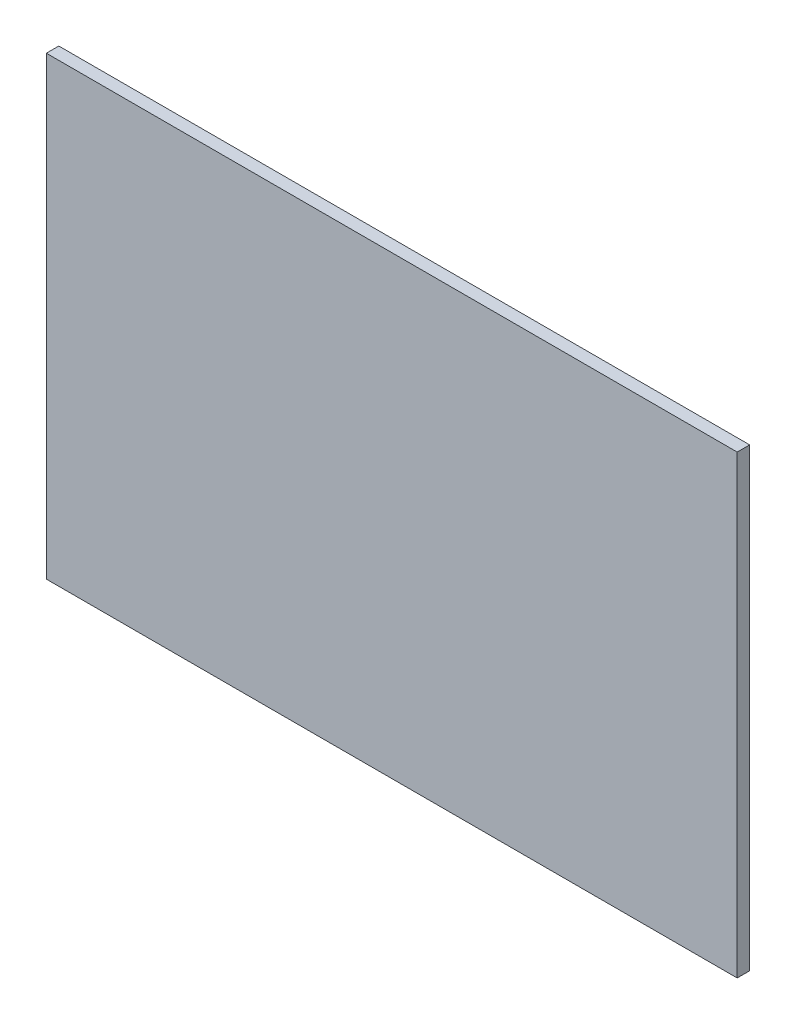
SolidWorks part; units mm, degrees
other "DetailItem1"
ref_plane "Front Plane" through (0, 0, 0) normal (0, 0, 1) x (1, 0, 0)
ref_plane "Top Plane" through (0, 0, 0) normal (0, 1, 0) x (1, 0, 0)
ref_plane "Right Plane" through (0, 0, 0) normal (1, 0, 0) x (0, 0, -1)
sketch "Sketch1" plane through (0, 0, 0) normal (0, 0, 1) x (1, 0, 0)
  line L0 (0, 1.905) -> (13.335, 1.905)
  line L1 (0, 0) -> (91.5, 0)
  line L2 (0, 0) -> (0, 60.325)
  line L3 (0, 60.325) -> (91.5, 60.325)
  line L4 (91.5, 0) -> (91.5, 60.325)
  line L5 (13.335, 1.905) -> (13.335, 19.685)
  line L6 (13.335, 19.685) -> (0, 19.685)
  line L7 (0, 21.59) -> (13.335, 21.59)
  line L8 (13.335, 21.59) -> (13.335, 39.37)
  line L9 (13.335, 39.37) -> (0, 39.37)
  line L10 (91.5, 36.195) -> (78.165, 36.195)
  line L11 (78.165, 36.195) -> (78.165, 53.975)
  line L12 (78.165, 53.975) -> (91.5, 53.975)
  line L13 (0, 57.531) -> (14.224, 57.531)
  line L14 (14.224, 57.531) -> (14.224, 42.799)
  line L15 (14.224, 42.799) -> (0, 42.799)
  dimension "D1" = 60.325
  dimension "D2" = 91.5
  dimension "D3" = 17.78
  dimension "D4" = 17.78
  dimension "D5" = 1.905
  dimension "D6" = 13.335
  dimension "D7" = 1.905
  dimension "D8" = 17.78
  dimension "D9" = 36.195
  dimension "D10" = 14.224
  dimension "D11" = 14.732
  dimension "D12" = 42.799
extrude "Boss-Extrude1" add sketch "Sketch1" along normal blind 1.65 contours L14 L15 L2 L9 L8 L7 L6 L5 L0 L1 L4 L10 L11 L12 L3 L13 | L15 L14 L13 L2 | L8 L9 L2 L7 | L5 L6 L2 L0 | L12 L11 L10 L4
